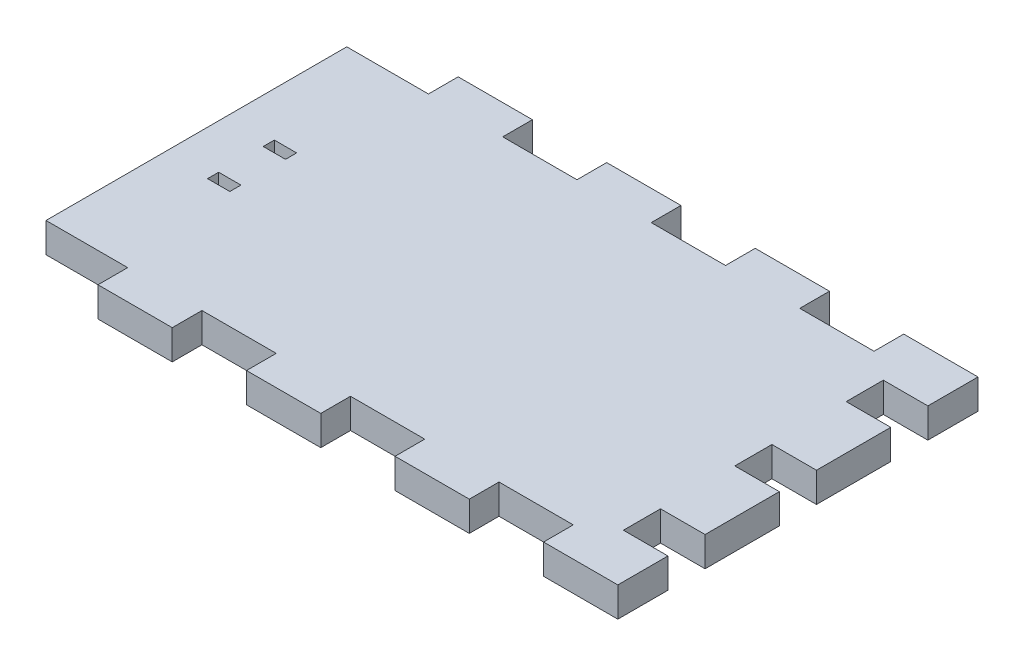
SolidWorks part; units mm, degrees
material "Maple"
ref_plane "Front Plane" through (0, 0, 0) normal (0, 0, 1) x (1, 0, 0)
ref_plane "Top Plane" through (0, 0, 0) normal (0, 1, 0) x (1, 0, 0)
ref_plane "Right Plane" through (0, 0, 0) normal (1, 0, 0) x (0, 0, -1)
sketch "Sketch1" plane through (0, 0, 0) normal (0, 1, 0) x (1, 0, 0)
  line L1 (0, 0) -> (75, 0)
  line L2 (0, 0) -> (0, -40.5)
  line L3 (0, -40.5) -> (75, -40.5)
  line L4 (75, 0) -> (75, -40.5)
  dimension "D1" = 75
  dimension "D2" = 40.5
extrude "Boss-Extrude1" add sketch "Sketch1" along normal blind 4
sketch "Sketch2" plane through (75, 0, 0) normal (1, 0, 0) x (0, 0, -1)
  line L0 (-40.5, 4) -> (-40.5, 0) construction
  line L1 (-40.5, 4) -> (-37.75, 4)
  line L2 (-40.5, 4) -> (-40.5, 0)
  line L3 (-40.5, 0) -> (-37.75, 0)
  line L4 (-37.75, 4) -> (-37.75, 0)
  line L5 (-40.5, 4) -> (0, 4) construction
  line L6 (-40.5, 0) -> (0, 0) construction
  line L7 (0, 4) -> (0, 0) construction
  line L8 (-32.75, 4) -> (-22.75, 4)
  line L9 (-32.75, 4) -> (-32.75, 0)
  line L10 (-32.75, 0) -> (-22.75, 0)
  line L11 (-22.75, 4) -> (-22.75, 0)
  line L12 (-17.75, 4) -> (-7.75, 4)
  line L13 (-17.75, 4) -> (-17.75, 0)
  line L14 (-17.75, 0) -> (-7.75, 0)
  line L15 (-7.75, 4) -> (-7.75, 0)
  line L16 (-2.75, 4) -> (0, 4)
  line L17 (-2.75, 4) -> (-2.75, 0)
  line L18 (-2.75, 0) -> (0, 0)
  line L19 (0, 4) -> (0, 0)
  dimension "D1" = 2.75
  dimension "D2" = 5
  dimension "D3" = 5
  dimension "D4" = 5
  dimension "D5" = 10
  dimension "D6" = 2.75
extrude "Boss-Extrude2" add sketch "Sketch2" along normal blind 6
sketch "Sketch3" plane through (0, 4, 0) normal (0, 1, 0) x (1, 0, 0)
  line L0 (81, 0) -> (0, 0) construction
  line L1 (81, 0) -> (71, 0)
  line L2 (81, 0) -> (81, 4)
  line L3 (81, 4) -> (71, 4)
  line L4 (71, 0) -> (71, 4)
  line L5 (81, -40.5) -> (71, -40.5)
  line L6 (81, -40.5) -> (81, -44.5)
  line L7 (81, -44.5) -> (71, -44.5)
  line L8 (71, -40.5) -> (71, -44.5)
  dimension "D1" = 4
  dimension "D2" = 10
extrude "Boss-Extrude3" add sketch "Sketch3" against normal through all
pattern_linear "LPattern1" count 4 spacing 20 along (-1, 0, 0) of "Boss-Extrude3"
sketch "Sketch4" plane through (0, 4, 0) normal (0, 1, 0) x (1, 0, 0)
  line L0 (0, -20.25) -> (81, -20.25) construction
  line L1 (0, 0) -> (0, -40.5) construction
  line L3 (6, -23.25) -> (9, -23.25)
  line L4 (6, -23.25) -> (6, -24.75)
  line L5 (6, -24.75) -> (9, -24.75)
  line L6 (9, -23.25) -> (9, -24.75)
  line L7 (6, -17.25) -> (9, -17.25)
  line L8 (6, -17.25) -> (6, -15.75)
  line L9 (6, -15.75) -> (9, -15.75)
  line L10 (9, -17.25) -> (9, -15.75)
  dimension "D1" = 3
  dimension "D2" = 1.5
  dimension "D3" = 3
  dimension "D4" = 6
  dimension "D5" = 3
  dimension "D6" = 3
extrude "Cut-Extrude1" cut sketch "Sketch4" against normal through all
equation "\"D5@Sketch4\"=\"D3@Sketch4\""
equation "\"D6@Sketch4\"=\"D1@Sketch4\""
